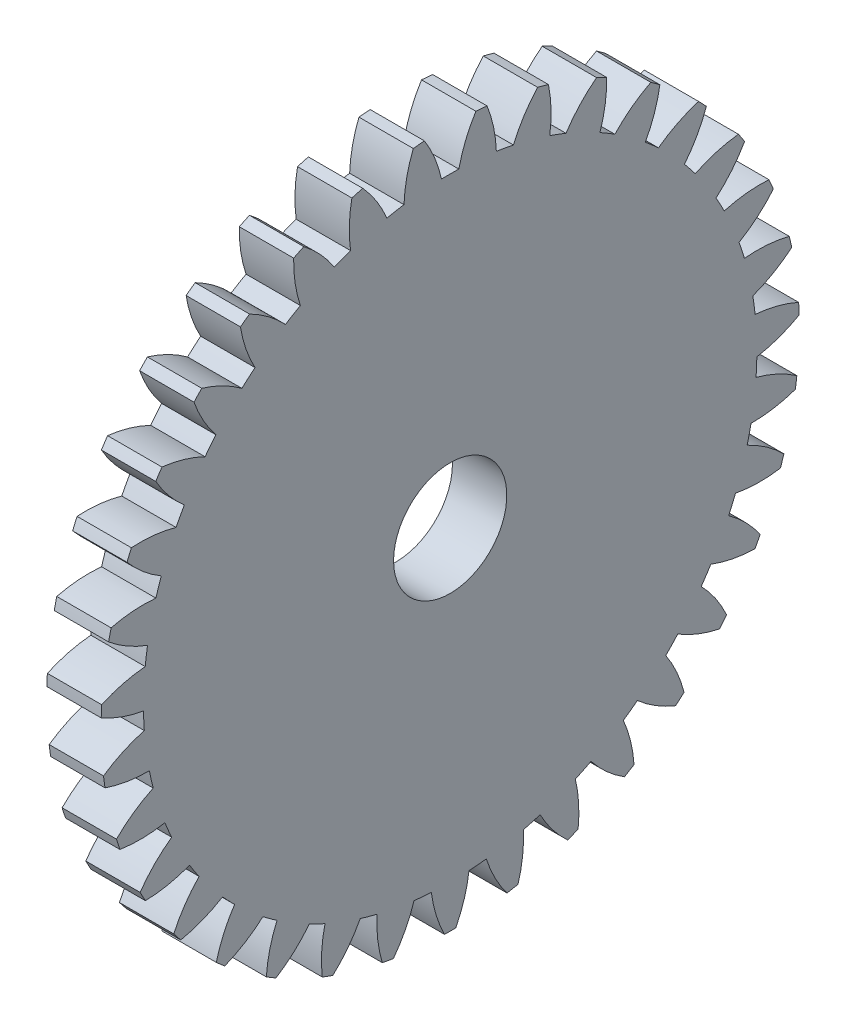
SolidWorks part; units mm, degrees
ref_plane "Plane1" through (0, 0, 0) normal (0, 0, 1) x (1, 0, 0)
ref_plane "Plane2" through (0, 0, 0) normal (0, 1, 0) x (1, 0, 0)
ref_plane "Plane3" through (0, 0, 0) normal (1, 0, 0) x (0, 0, -1)
sketch "HoldingSke" plane through (0, 0, 0) normal (0, 1, 0) x (1, 0, 0)
  line L0 (0, 0) -> (499.3551, -349.6522)
  line L1 (-15, 0) -> (100, 0) construction
  line L2 (0, 0) -> (-2.1039, 2.3779)
  line L3 (0, 0) -> (-11.863, 4.5341)
  line L4 (0, 0) -> (7.0742, 4.9534)
  line L5 (0, 0) -> (-47.5972, -17.7524)
  line L6 (0, 0) -> (-2.5267, -1.7048)
  line L7 (-2.1039, 2.3779) -> (8.8308, 51.9871)
  line L8 (-76.2, 54.61) -> (-69.596, 54.61)
  line L9 (-71.009, 38.7566) -> (-53.1078, 45.2721)
  line L10 (-76.2, 71.12) -> (104.1128, 71.12)
  line L11 (0, 0) -> (-3.048, 0)
  line L12 (-76.2, 101.6) -> (-76.1573, 101.6)
  line L13 (24.9733, 27.94) -> (52.9518, 28.4284)
  line L14 (24.9733, 27.94) -> (25.0241, 27.9398)
  line L15 (24.9733, 27.94) -> (100.4021, 29.52)
  circle A0 centre (0, 0) radius 3.175
  circle A1 centre (0, 0) radius 17.2
  circle A2 centre (0, 0) radius 38.1
  circle A3 centre (0, 0) radius 3.175
  dimension "MHD" = 34.4001
  dimension "Hub_dia" = 76.2
  dimension "Bore" = 6.35
  dimension "MBD" = 6.35
  dimension "Num_teeth" = 35
  dimension "Pitch_radius" = 180.3128
  dimension "Pitch" = 609.6
  dimension "Width" = 3.048
  dimension "Overall_len" = 50.8
  dimension "Show_teeth" = 35
  dimension "Thickness" = 3.048
  dimension "OAL" = 50.8001
  dimension "T_dim" = 6.604
  dimension "Ap" = 20
  dimension "H" = 19.05
  dimension "Backlash" = 0.0427
  dimension "Addendum_fac" = 1
  dimension "Dedendum_fac" = 1.2
  dimension "Clearance_fac" = 0.2
  dimension "Dedendum_add" = 0.0508
sketch "BasProSke" plane through (0, 0, 0) normal (0, 1, 0) x (1, 0, 0)
  line L0 (-10, 0) -> (60, 0) construction
  line L1 (0, 0) -> (0, 19.5792)
  line L2 (0, 0) -> (3.048, 0)
  line L3 (3.048, 0) -> (3.048, 19.5792)
  line L4 (3.048, 19.5792) -> (0, 19.5792)
  dimension "Diameter" = 39.1583
  dimension "Thickness" = 3.048
revolve "Base-Revolve" add sketch "BasProSke" angle 360 about L0
sketch "TooCutSke" plane through (0, 0, 0) normal (1, 0, 0) x (0, 0, -1)
  line L1 (0, 0) -> (0, 107) construction
  line L2 (0, 0) -> (-0.9056, 18.4987) construction
  line L3 (0, 0) -> (-3.3176, 36.8618) construction
  line L4 (-0.9056, 18.4987) -> (-1.6588, 18.4309) construction
  arc A0 (0.4877, 17.1931) -> (-0.4877, 17.1931) centre (0, 0) ccw
  arc A1 (1.4567, 19.5504) -> (-1.4567, 19.5504) centre (0, 0) ccw
  circle A2 centre (0, 0) radius 18.5208 construction
  circle A3 centre (0, 0) radius 17.4039 construction
  arc A4 (-0.4877, 17.1931) -> (-1.4567, 19.5504) centre (-7.722, 15.597) ccw
  arc A5 (1.4567, 19.5504) -> (0.4877, 17.1931) centre (7.722, 15.597) ccw
  dimension "Root_dia" = 34.4001
  dimension "Overcut_dia" = 39.2091
  dimension "Pitch_dia" = 37.0417
  dimension "Base_dia" = 34.8078
  dimension "Flank_rad" = 7.4083
  dimension "Half_ang" = 5.143
  dimension "Half_CT" = 0.7563
extrude "ToothCut" cut sketch "TooCutSke" along normal through all
fillet "Breaks" [suppressed] radius 0.0212
fillet "RootFillets" [suppressed] radius 0.2625
pattern_circular "TeethCuts" count 35 every 10.286 about axis through (-10, 0, 0) along (1, 0, 0) of "ToothCut", "RootFillets", "Breaks"
sketch "HubNeaOneSke" plane through (0, 0, 0) normal (-1, 0, 0) x (0, 0, 1)
  circle A0 centre (0, 0) radius 17.2
  dimension "Diameter" = 34.4001
extrude "HubNearOne" [suppressed] add sketch "HubNeaOneSke" along normal blind 47.7521
sketch "HubNeaBotSke" plane through (0, 0, 0) normal (-1, 0, 0) x (0, 0, 1)
  circle A0 centre (0, 0) radius 17.2
  dimension "Diameter" = 34.4001
extrude "HubNearBoth" [suppressed] add sketch "HubNeaBotSke" along normal blind 23.876
ref_plane "FarPln" through (3.048, 0, 0) normal (1, 0, 0) x (0, 0, -1)
sketch "HubFarSke" plane through (3.048, 0, 0) normal (1, 0, 0) x (0, 0, -1)
  circle A0 centre (0, 0) radius 17.2
  dimension "Diameter" = 34.4001
extrude "HubFar" [suppressed] add sketch "HubFarSke" along normal blind 23.876
sketch "BorSke" plane through (0, 0, 0) normal (1, 0, 0) x (0, 0, -1)
  circle A0 centre (0, 0) radius 3.175
  dimension "Diameter" = 6.35
extrude "Bore" cut sketch "BorSke" along normal mid plane 101.6001
sketch "KeySke" plane through (0, 0, 0) normal (1, 0, 0) x (0, 0, -1)
  line L0 (-0.127, 0) -> (-0.127, 3.429)
  line L1 (-0.127, 3.429) -> (0.127, 3.429)
  line L2 (0.127, 3.429) -> (0.127, 0)
  line L3 (0, 0) -> (0, 34) construction
  line L4 (-0.127, 0) -> (0.127, 0)
  dimension "Offset" = 3.429
  dimension "Width" = 0.254
extrude "Keyway" [suppressed] cut sketch "KeySke" along normal mid plane 101.6001
pattern_circular "Keyway2" [suppressed] count 2 every 90 about axis through (-10, 0, 0) along (1, 0, 0)
equation "' \"Pitch@HoldingSke\" = 4"
equation "' \"Num_teeth@HoldingSke\" = 12"
equation "' \"Ap@HoldingSke\" =  20"
equation "' \"Width@HoldingSke\" = 0.5"
equation "' \"Hub_dia@HoldingSke\"= 1"
equation "' \"Overall_len@HoldingSke\" = 1.0"
equation "' \"Bore@HoldingSke\" = 0.75"
equation "' \"T_dim@HoldingSke\" = 0.85"
equation "' \"Width@KeySke\" = 0.25"
equation "' \"Show_teeth@HoldingSke\" = 13"
equation "' \"Backlash@HoldingSke\" = 0.009"
equation "' \"Addendum_fac@HoldingSke\" = 1.0"
equation "' \"Dedendum_fac@HoldingSke\" = 1.25"
equation "' \"Dedendum_add@HoldingSke\" = 0.00005"
equation "' \"Clearance_fac@HoldingSke\" = 0.25"
equation "' \"Pitch@HoldingSke\" = 0.5"
equation "' \"Num_teeth@HoldingSke\" = 23"
equation "' \"Show_teeth@HoldingSke\" = 23"
equation "' \"Backlash@HoldingSke\" = 0.0375"
equation "\"Overcut_dia@TooCutSke\" = (\"Num_teeth@HoldingSke\" + 2 * \"Addendum_fac@HoldingSke\") / \"Pitch@HoldingSke\" + 0.002"
equation "\"Pitch_dia@TooCutSke\" = \"Num_teeth@HoldingSke\" / \"Pitch@HoldingSke\""
equation "\"Base_dia@TooCutSke\" = \"Num_teeth@HoldingSke\" / \"Pitch@HoldingSke\" * cos((\"Ap@HoldingSke\"  * 3.14159265 / 180))"
equation "\"Root_dia@TooCutSke\" = (\"Num_teeth@HoldingSke\" + 2) / \"Pitch@HoldingSke\" - 2 * (\"Addendum_fac@HoldingSke\" + \"Dedendum_fac@HoldingSke\") / \"Pitch@HoldingSke\" - \"Dedendum_add@HoldingSke\" * 2"
equation "\"Half_ang@TooCutSke\" = 180 / \"Num_teeth@HoldingSke\""
equation "\"Half_CT@TooCutSke\" = \"Num_teeth@HoldingSke\" / \"Pitch@HoldingSke\" * sin((3.14159265 / 2 / \"Num_teeth@HoldingSke\")) / 2 - 7 * \"Backlash@HoldingSke\" / 4"
equation "\"Flank_rad@TooCutSke\" = \"Num_teeth@HoldingSke\" / \"Pitch@HoldingSke\" / 5"
equation "\"Radius@RootFillets\" = \"Clearance_fac@HoldingSke\" / \"Pitch@HoldingSke\" + \"Dedendum_add@HoldingSke\""
equation "\"Break_rad@Breaks\" = 0.02 / \"Pitch@HoldingSke\""
equation "\"Thickness@HoldingSke\" = \"Width@HoldingSke\""
equation "\"OAL@HoldingSke\" = \"Thickness@HoldingSke\""
equation "\"MHD@HoldingSke\" = (\"Num_teeth@HoldingSke\" + 2) / \"Pitch@HoldingSke\" - 2 * (\"Addendum_fac@HoldingSke\" + \"Dedendum_fac@HoldingSke\")  / \"Pitch@HoldingSke\" - \"Dedendum_add@HoldingSke\" * 2"
equation "\"MBD@HoldingSke\" = (\"Num_teeth@HoldingSke\" + 2) / \"Pitch@HoldingSke\" - 2 * (\"Addendum_fac@HoldingSke\" + \"Dedendum_fac@HoldingSke\")  / \"Pitch@HoldingSke\" - \"Dedendum_add@HoldingSke\" * 2 - 0.002"
equation "\"MHD@HoldingSke\" = ((sgn( \"MHD@HoldingSke\" - \"Hub_dia@HoldingSke\" )-1)*( \"MHD@HoldingSke\" - \"Hub_dia@HoldingSke\" ))/-2+ \"Hub_dia@HoldingSke\""
equation "\"MBD@HoldingSke\" = ((sgn( \"MBD@HoldingSke\" - \"Bore@HoldingSke\" )-1)*( \"MBD@HoldingSke\" - \"Bore@HoldingSke\" ))/-2+ \"Bore@HoldingSke\""
equation "\"OAL@HoldingSke\" = ((sgn( \"OAL@HoldingSke\" - \"Overall_len@HoldingSke\" )+1)*( \"OAL@HoldingSke\" - \"Overall_len@HoldingSke\" ))/2 + \"Overall_len@HoldingSke\" + 0.000002"
equation "\"Num_teeth@TeethCuts\" = int( \"Show_teeth@HoldingSke\" ) + 1"
equation "\"Num_teeth@TeethCuts\" = ((sgn( \"Num_teeth@TeethCuts\" - \"Num_teeth@HoldingSke\" )-1)*( \"Num_teeth@TeethCuts\" - \"Num_teeth@HoldingSke\" ))/-2+ \"Num_teeth@HoldingSke\""
equation "\"Num_teeth@TeethCuts\" = ((sgn( \"Num_teeth@TeethCuts\" - 2.0)+1)*( \"Num_teeth@TeethCuts\" - 2.0))/2 +2.0"
equation "\"Angle@TeethCuts\" = 360.0 / \"Num_teeth@HoldingSke\""
equation "\"Diameter@BasProSke\" = (\"Num_teeth@HoldingSke\" + 2 * \"Addendum_fac@HoldingSke\") / \"Pitch@HoldingSke\""
equation "\"Thickness@BasProSke\"  = \"Thickness@HoldingSke\""
equation "' \"Fillet_rad@BasProSke\" =  \"Thickness@HoldingSke\" * 0.05"
equation "\"MHD@HoldingSke\" = ((sgn( \"MHD@HoldingSke\" - \"Root_dia@TooCutSke\" )-1)*( \"MHD@HoldingSke\" - \"Root_dia@TooCutSke\" ))/-2+ \"Root_dia@TooCutSke\""
equation "\"Diameter@HubNeaOneSke\" = \"MHD@HoldingSke\""
equation "\"Length@HubNearOne\" = \"OAL@HoldingSke\" - \"Thickness@BasProSke\""
equation "\"Diameter@HubNeaBotSke\" = \"MHD@HoldingSke\""
equation "\"Length@HubNearBoth\" = ( \"OAL@HoldingSke\" - \"Thickness@BasProSke\" ) / 2.0"
equation "\"Thickness@FarPln\" = \"Thickness@BasProSke\""
equation "\"Diameter@HubFarSke\" = \"MHD@HoldingSke\""
equation "\"Length@HubFar\" = ( \"OAL@HoldingSke\" - \"Thickness@BasProSke\" ) / 2.0"
equation "\"Diameter@BorSke\" = \"MBD@HoldingSke\""
equation "\"D1@Bore\" = \"OAL@HoldingSke\" * 2.0"
equation "\"D1@Keyway\" = \"OAL@HoldingSke\" * 2.0"
equation "\"Offset@KeySke\" = \"T_dim@HoldingSke\" - \"MBD@HoldingSke\" / 2.0"
